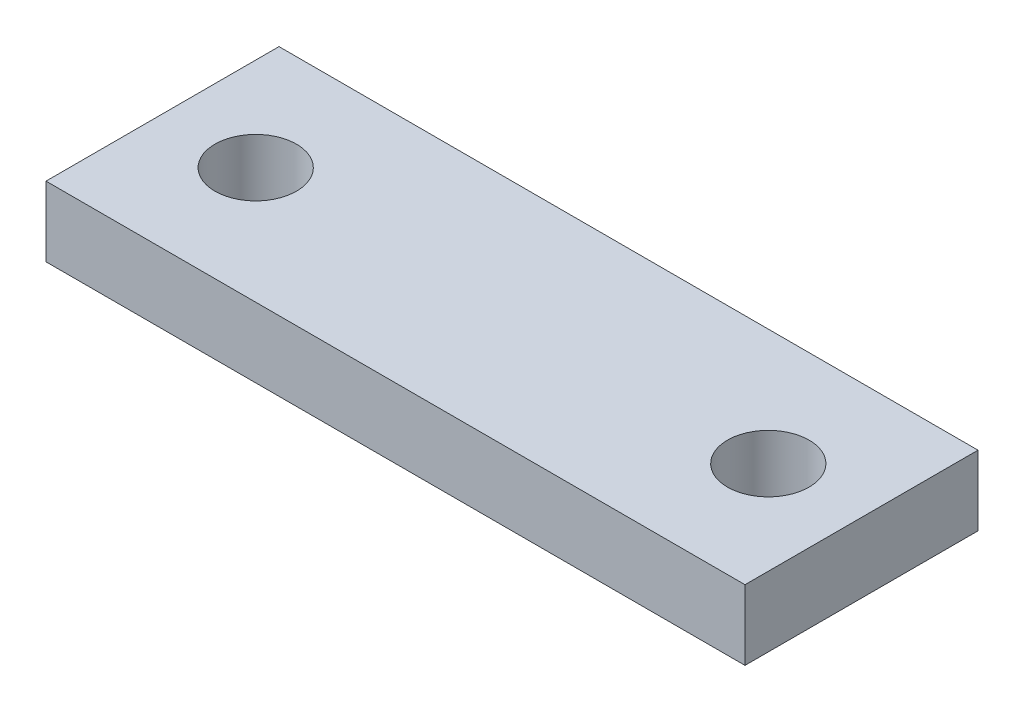
SolidWorks part; units mm, degrees
material "ABS PC"
ref_plane "Front Plane" through (0, 0, 0) normal (0, 0, 1) x (1, 0, 0)
ref_plane "Top Plane" through (0, 0, 0) normal (0, 1, 0) x (1, 0, 0)
ref_plane "Right Plane" through (0, 0, 0) normal (1, 0, 0) x (0, 0, -1)
sketch "Sketch1" plane through (0, 0, 0) normal (0, 1, 0) x (1, 0, 0)
  line L0 (0, 0) -> (0, 10)
  line L1 (0, 0) -> (30, 0)
  line L2 (0, 10) -> (30, 10)
  line L3 (30, 0) -> (30, 10)
  circle A0 centre (4, 5) radius 1.75
  circle A1 centre (26, 5) radius 1.75
  dimension "D3" = 3.5
  dimension "D5" = 22
  dimension "D6" = 4
  dimension "D1" = 10
  dimension "D2" = 30
  dimension "D4" = 5
extrude "Boss-Extrude1" add sketch "Sketch1" along normal blind 3
